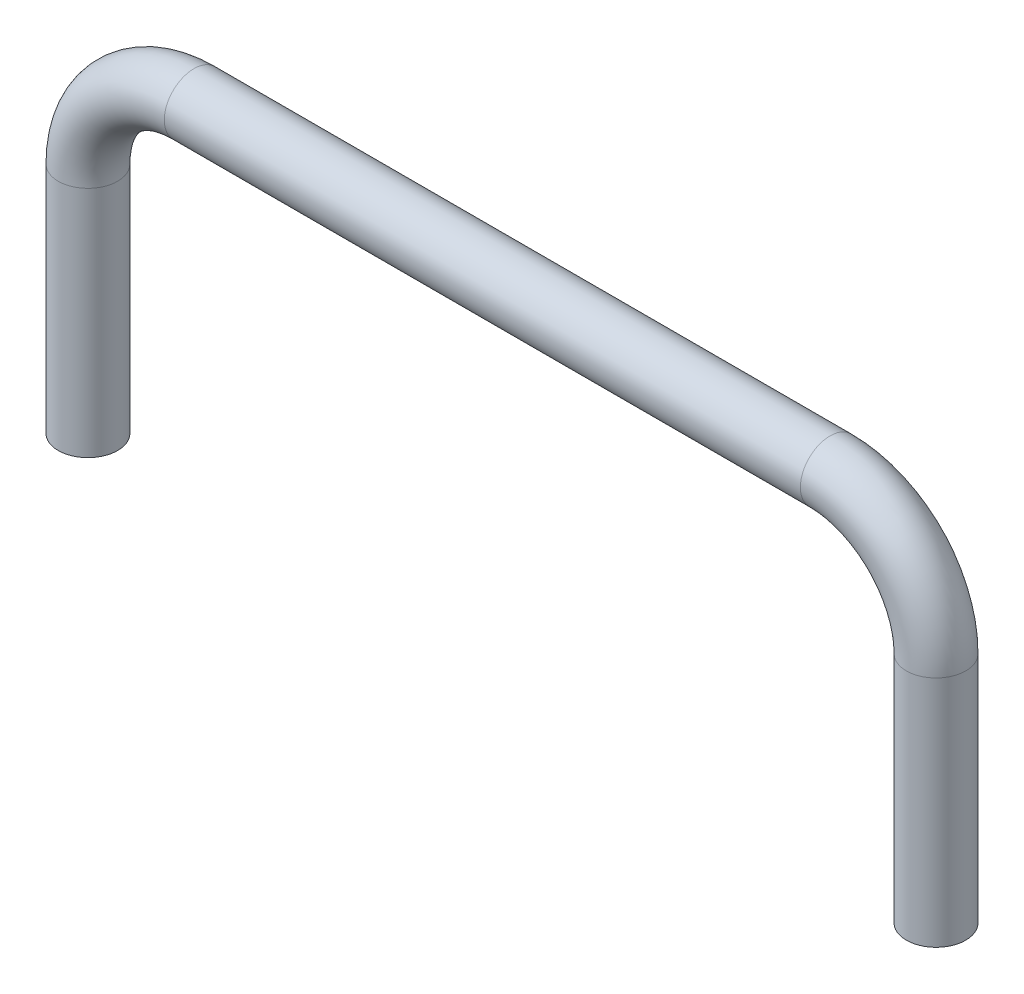
SolidWorks part; units mm, degrees
ref_plane "Front Plane" through (0, 0, 0) normal (0, 0, 1) x (1, 0, 0)
ref_plane "Top Plane" through (0, 0, 0) normal (0, 1, 0) x (1, 0, 0)
ref_plane "Right Plane" through (0, 0, 0) normal (1, 0, 0) x (0, 0, -1)
sketch "Sketch1" plane through (0, 0, 0) normal (0, 0, 1) x (1, 0, 0)
  line L0 (0, 0) -> (0, 5.5)
  line L1 (2.5, 8) -> (17.5, 8)
  line L2 (20, 5.5) -> (20, 0)
  arc A0 (0, 5.5) -> (2.5, 8) centre (2.5, 5.5) cw
  arc A1 (17.5, 8) -> (20, 5.5) centre (17.5, 5.5) cw
  point P1 (0, 0)
  dimension "D4" = 2.5
  dimension "D5" = 2.5
  dimension "D1" = 5.5
  dimension "D2" = 5.5
  dimension "D3" = 20
sketch "Sketch2" plane through (0, 0, 0) normal (0, 1, 0) x (1, 0, 0)
  circle A0 centre (0, 0) radius 0.7
  dimension "D1" = 1.4
sweep "Sweep1" add profiles "Sketch2" path "Sketch1"
